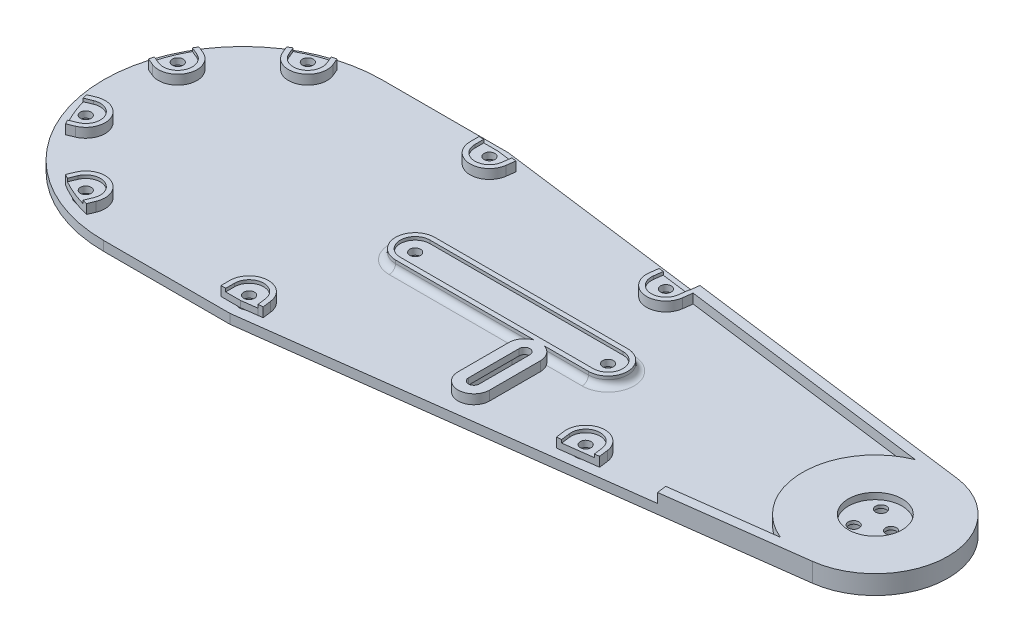
SolidWorks part; units mm, degrees
ref_plane "Front Plane" through (0, 0, 0) normal (0, 0, 1) x (1, 0, 0)
ref_plane "Top Plane" through (0, 0, 0) normal (0, 1, 0) x (1, 0, 0)
ref_plane "Right Plane" through (0, 0, 0) normal (1, 0, 0) x (0, 0, -1)
sketch "Sketch1" plane through (0, 0, 0) normal (0, 1, 0) x (1, 0, 0)
  line L0 (0, 0) -> (200, 0) construction
  line L1 (0, 44) -> (40, 44)
  line L2 (40, 44) -> (202.9659, 22.808)
  line L3 (40, -44) -> (202.9659, -22.808)
  line L4 (0, -44) -> (40, -44)
  line L5 (0, 0) -> (-44, 0) construction
  line L6 (0, 0) -> (-35.1074, 14.542) construction
  line L7 (40, 44) -> (40, -44) construction
  line L8 (44.096, 37.4168) -> (108.6418, 29.0233) construction
  line L9 (109.4155, 34.9732) -> (108.6418, 29.0233) construction
  line L10 (139.1651, -31.1046) -> (137.342, -17.0851) construction
  line L11 (44.2573, -37.3959) -> (129.8631, -26.2637) construction
  arc A0 (0, 44) -> (0, -44) centre (0, 0) ccw
  arc A1 (202.9659, -22.808) -> (202.9659, 22.808) centre (200, 0) ccw
  circle A2 centre (-35.1074, 14.542) radius 1.7
  circle A3 centre (-14.542, 35.1074) radius 1.7
  circle A4 centre (14.542, 35.1074) radius 1.7 [skipped]
  circle A5 centre (35.1074, 14.542) radius 1.7 [skipped]
  circle A6 centre (35.1074, -14.542) radius 1.7 [skipped]
  circle A7 centre (14.542, -35.1074) radius 1.7 [skipped]
  circle A8 centre (-14.542, -35.1074) radius 1.7
  circle A9 centre (-35.1074, -14.542) radius 1.7
  circle A10 centre (200, 0) radius 10.5 construction
  circle A11 centre (40, 38) radius 1.7
  circle A12 centre (40, -38) radius 1.7
  circle A15 centre (40, 38) radius 4.3 construction
  circle A17 centre (40, -38) radius 4.3 construction
  circle A18 centre (134.1272, -25.7092) radius 1.7
  circle A19 centre (134.1272, -25.7092) radius 4.3 construction
  circle A20 centre (87.0602, -31.8298) radius 1.7 construction
  circle A21 centre (104.1794, 29.6036) radius 1.7
  circle A22 centre (104.1794, 29.6036) radius 4.5 construction
  point P29 (0, 0)
  dimension "D1" = 88
  dimension "D3" = 46
  dimension "D6" = 3.4
  dimension "D9" = 21
  dimension "D13" = 9
  dimension "D14" = 8.6
  dimension "D15" = 8.6
  dimension "D18" = 8.6
  dimension "D2" = 200
  dimension "D4" = 40
  dimension "D5" = 22.5
  dimension "D7" = 38
  dimension "D8" = 8
  dimension "D10" = 38
  dimension "D11" = 6
  dimension "D12" = 70
  dimension "D16" = 100
  dimension "D17" = 6
extrude "Boss-Extrude1" add sketch "Sketch1" along normal blind 3
sketch "Sketch2" plane through (0, 3, 0) normal (0, 1, 0) x (1, 0, 0)
  line L0 (202.5533, 19.6347) -> (39.7928, 40.8) construction
  line L1 (39.7928, 40.8) -> (0, 40.8) construction
  line L2 (0, -40.8) -> (39.7928, -40.8) construction
  line L3 (39.7928, -40.8) -> (202.5533, -19.6347) construction
  line L4 (0, -44) -> (40, -44)
  line L5 (40, -44) -> (202.9659, -22.808)
  line L6 (202.9659, 22.808) -> (40, 44)
  line L7 (40, 44) -> (0, 44)
  line L8 (0, -44) -> (40, -44) construction
  line L9 (40, -44) -> (202.9659, -22.808) construction
  line L10 (202.9659, 22.808) -> (40, 44) construction
  line L11 (40, 44) -> (0, 44) construction
  line L12 (-33.3471, 18.7918) -> (-35.6936, 19.7638)
  line L13 (0, 0) -> (-35.1074, 14.542) construction
  line L14 (-36.8678, 10.2921) -> (-39.2143, 11.2641)
  line L15 (-32.7731, 20.1776) -> (-34.9362, 21.0737)
  line L16 (-37.4418, 8.9063) -> (-39.605, 9.8023)
  line L17 (-32.7731, 20.1776) -> (-35.1196, 21.1496) construction
  line L18 (-37.4418, 8.9063) -> (-39.7883, 9.8783) construction
  line L19 (-20.1776, 32.7731) -> (-21.0737, 34.9362)
  line L20 (-8.9063, 37.4418) -> (-9.8023, 39.605)
  line L21 (-10.2921, 36.8678) -> (-11.2641, 39.2143)
  line L22 (-18.7918, 33.3471) -> (-19.7638, 35.6936)
  line L23 (8.9063, 37.4418) -> (9.8023, 39.605) [skipped]
  line L24 (20.1776, 32.7731) -> (21.0737, 34.9362) [skipped]
  line L25 (18.7918, 33.3471) -> (19.7638, 35.6936) [skipped]
  line L26 (10.2921, 36.8678) -> (11.2641, 39.2143) [skipped]
  line L27 (32.7731, 20.1776) -> (34.9362, 21.0737) [skipped]
  line L28 (37.4418, 8.9063) -> (39.605, 9.8023) [skipped]
  line L29 (36.8678, 10.2921) -> (39.2143, 11.2641) [skipped]
  line L30 (33.3471, 18.7918) -> (35.6936, 19.7638) [skipped]
  line L31 (37.4418, -8.9063) -> (39.605, -9.8023) [skipped]
  line L32 (32.7731, -20.1776) -> (34.9362, -21.0737) [skipped]
  line L33 (33.3471, -18.7918) -> (35.6936, -19.7638) [skipped]
  line L34 (36.8678, -10.2921) -> (39.2143, -11.2641) [skipped]
  line L35 (20.1776, -32.7731) -> (21.0737, -34.9362) [skipped]
  line L36 (8.9063, -37.4418) -> (9.8023, -39.605) [skipped]
  line L37 (10.2921, -36.8678) -> (11.2641, -39.2143) [skipped]
  line L38 (18.7918, -33.3471) -> (19.7638, -35.6936) [skipped]
  line L39 (-8.9063, -37.4418) -> (-9.8023, -39.605)
  line L40 (-20.1776, -32.7731) -> (-21.0737, -34.9362)
  line L41 (-18.7918, -33.3471) -> (-19.7638, -35.6936)
  line L42 (-10.2921, -36.8678) -> (-11.2641, -39.2143)
  line L43 (-32.7731, -20.1776) -> (-34.9362, -21.0737)
  line L44 (-37.4418, -8.9063) -> (-39.605, -9.8023)
  line L45 (-36.8678, -10.2921) -> (-39.2143, -11.2641)
  line L46 (-33.3471, -18.7918) -> (-35.6936, -19.7638)
  line L47 (0, 0) -> (200, 0) construction
  line L48 (40, 44) -> (40, 0) construction
  line L49 (44.5616, 37.4068) -> (44.9162, 40.1338)
  line L50 (35.4, 38) -> (35.4, 40.8)
  line L51 (99.6178, 30.1968) -> (99.9789, 32.9734)
  line L52 (108.741, 29.0104) -> (109.1021, 31.787)
  line L55 (129.5656, -26.3024) -> (129.9267, -29.079)
  line L56 (138.6888, -25.116) -> (139.0499, -27.8926)
  line L57 (33.9, 38) -> (33.9, 40.8)
  line L58 (46.0491, 37.2134) -> (46.4037, 39.9403)
  line L59 (98.1303, 30.3902) -> (98.4914, 33.1669)
  line L60 (110.2285, 28.817) -> (110.5895, 31.5936)
  line L61 (140.1763, -24.9226) -> (140.5374, -27.6992)
  line L62 (128.0782, -26.4958) -> (128.4392, -29.2724)
  line L65 (33.9, 40.8) -> (35.4, 40.8)
  line L66 (44.9162, 40.1338) -> (46.4037, 39.9403)
  line L67 (44.5616, -37.4068) -> (44.9162, -40.1338)
  line L68 (35.4, -38) -> (35.4, -40.8)
  line L69 (33.9, -40.8) -> (35.4, -40.8)
  line L70 (33.9, -38) -> (33.9, -40.8)
  line L71 (46.0491, -37.2134) -> (46.4037, -39.9403)
  line L72 (44.9162, -40.1338) -> (46.4037, -39.9403)
  line L75 (128.4392, -29.2724) -> (129.9267, -29.079)
  line L76 (139.0499, -27.8926) -> (140.5374, -27.6992)
  line L77 (98.4914, 33.1669) -> (99.9789, 32.9734)
  line L78 (109.1021, 31.787) -> (110.5895, 31.5936)
  arc A0 (0, 40.8) -> (0, -40.8) centre (0, 0) ccw construction
  arc A1 (-36.8678, 10.2921) -> (-33.3471, 18.7918) centre (-35.1074, 14.542) ccw
  arc A2 (0, 44) -> (0, -44) centre (0, 0) ccw
  arc A3 (202.9659, -22.808) -> (202.9659, 22.808) centre (200, 0) ccw
  arc A5 (0, 44) -> (0, -44) centre (0, 0) ccw construction
  arc A6 (-37.4418, 8.9063) -> (-32.7731, 20.1776) centre (-35.1074, 14.542) ccw
  arc A7 (-39.605, 9.8023) -> (-39.2143, 11.2641) centre (0, 0) cw
  arc A8 (-34.9362, 21.0737) -> (-35.6936, 19.7638) centre (0, 0) ccw
  arc A9 (-21.0737, 34.9362) -> (-19.7638, 35.6936) centre (0, 0) cw
  arc A10 (-20.1776, 32.7731) -> (-8.9063, 37.4418) centre (-14.542, 35.1074) ccw
  arc A11 (-9.8023, 39.605) -> (-11.2641, 39.2143) centre (0, 0) ccw
  arc A12 (-18.7918, 33.3471) -> (-10.2921, 36.8678) centre (-14.542, 35.1074) ccw
  arc A13 (9.8023, 39.605) -> (11.2641, 39.2143) centre (0, 0) cw [skipped]
  arc A14 (8.9063, 37.4418) -> (20.1776, 32.7731) centre (14.542, 35.1074) ccw [skipped]
  arc A15 (21.0737, 34.9362) -> (19.7638, 35.6936) centre (0, 0) ccw [skipped]
  arc A16 (10.2921, 36.8678) -> (18.7918, 33.3471) centre (14.542, 35.1074) ccw [skipped]
  arc A17 (34.9362, 21.0737) -> (35.6936, 19.7638) centre (0, 0) cw [skipped]
  arc A18 (32.7731, 20.1776) -> (37.4418, 8.9063) centre (35.1074, 14.542) ccw [skipped]
  arc A19 (39.605, 9.8023) -> (39.2143, 11.2641) centre (0, 0) ccw [skipped]
  arc A20 (33.3471, 18.7918) -> (36.8678, 10.2921) centre (35.1074, 14.542) ccw [skipped]
  arc A21 (39.605, -9.8023) -> (39.2143, -11.2641) centre (0, 0) cw [skipped]
  arc A22 (37.4418, -8.9063) -> (32.7731, -20.1776) centre (35.1074, -14.542) ccw [skipped]
  arc A23 (34.9362, -21.0737) -> (35.6936, -19.7638) centre (0, 0) ccw [skipped]
  arc A24 (36.8678, -10.2921) -> (33.3471, -18.7918) centre (35.1074, -14.542) ccw [skipped]
  arc A25 (21.0737, -34.9362) -> (19.7638, -35.6936) centre (0, 0) cw [skipped]
  arc A26 (20.1776, -32.7731) -> (8.9063, -37.4418) centre (14.542, -35.1074) ccw [skipped]
  arc A27 (9.8023, -39.605) -> (11.2641, -39.2143) centre (0, 0) ccw [skipped]
  arc A28 (18.7918, -33.3471) -> (10.2921, -36.8678) centre (14.542, -35.1074) ccw [skipped]
  arc A29 (-9.8023, -39.605) -> (-11.2641, -39.2143) centre (0, 0) cw
  arc A30 (-8.9063, -37.4418) -> (-20.1776, -32.7731) centre (-14.542, -35.1074) ccw
  arc A31 (-21.0737, -34.9362) -> (-19.7638, -35.6936) centre (0, 0) ccw
  arc A32 (-10.2921, -36.8678) -> (-18.7918, -33.3471) centre (-14.542, -35.1074) ccw
  arc A33 (-34.9362, -21.0737) -> (-35.6936, -19.7638) centre (0, 0) cw
  arc A34 (-32.7731, -20.1776) -> (-37.4418, -8.9063) centre (-35.1074, -14.542) ccw
  arc A35 (-39.605, -9.8023) -> (-39.2143, -11.2641) centre (0, 0) ccw
  arc A36 (-33.3471, -18.7918) -> (-36.8678, -10.2921) centre (-35.1074, -14.542) ccw
  arc A37 (35.4, 38) -> (44.5616, 37.4068) centre (40, 38) ccw
  circle A38 centre (40, 38) radius 1.7 construction
  arc A39 (99.6178, 30.1968) -> (108.741, 29.0104) centre (104.1794, 29.6036) ccw
  arc A41 (138.6888, -25.116) -> (129.5656, -26.3024) centre (134.1272, -25.7092) ccw
  arc A42 (33.9, 38) -> (46.0491, 37.2134) centre (40, 38) ccw
  arc A43 (98.1303, 30.3902) -> (110.2285, 28.817) centre (104.1794, 29.6036) ccw
  arc A44 (140.1763, -24.9226) -> (128.0782, -26.4958) centre (134.1272, -25.7092) ccw
  arc A46 (35.4, -38) -> (44.5616, -37.4068) centre (40, -38) cw
  arc A47 (33.9, -38) -> (46.0491, -37.2134) centre (40, -38) cw
  point P109 (0, 0)
  dimension "D3" = 9.2
  dimension "D1" = 0
  dimension "D2" = 3.2
  dimension "D4" = 1.5
  dimension "D6" = 1.5
  dimension "D5" = 8
extrude "Boss-Extrude2" add sketch "Sketch2" along normal blind 3
sketch "Sketch3" plane through (0, 3, 0) normal (0, 1, 0) x (1, 0, 0)
  line L0 (-36.8678, 10.2921) -> (-39.2143, 11.2641) construction
  line L1 (-35.6936, 19.7638) -> (-33.3471, 18.7918) construction
  line L2 (-36.8678, 10.2921) -> (-39.2143, 11.2641)
  line L3 (-35.6936, 19.7638) -> (-33.3471, 18.7918)
  line L4 (-11.2641, 39.2143) -> (-10.2921, 36.8678)
  line L5 (-18.7918, 33.3471) -> (-19.7638, 35.6936)
  line L6 (19.7638, 35.6936) -> (18.7918, 33.3471) [skipped]
  line L7 (10.2921, 36.8678) -> (11.2641, 39.2143) [skipped]
  line L8 (39.2143, 11.2641) -> (36.8678, 10.2921) [skipped]
  line L9 (33.3471, 18.7918) -> (35.6936, 19.7638) [skipped]
  line L10 (35.6936, -19.7638) -> (33.3471, -18.7918) [skipped]
  line L11 (36.8678, -10.2921) -> (39.2143, -11.2641) [skipped]
  line L12 (11.2641, -39.2143) -> (10.2921, -36.8678) [skipped]
  line L13 (18.7918, -33.3471) -> (19.7638, -35.6936) [skipped]
  line L14 (-19.7638, -35.6936) -> (-18.7918, -33.3471)
  line L15 (-10.2921, -36.8678) -> (-11.2641, -39.2143)
  line L16 (-39.2143, -11.2641) -> (-36.8678, -10.2921)
  line L17 (-33.3471, -18.7918) -> (-35.6936, -19.7638)
  line L18 (138.6888, -25.116) -> (139.0499, -27.8926) construction
  line L19 (129.9267, -29.079) -> (129.5656, -26.3024) construction
  line L20 (109.1021, 31.787) -> (108.741, 29.0104) construction
  line L21 (99.6178, 30.1968) -> (99.9789, 32.9734) construction
  line L24 (44.5616, -37.4068) -> (44.9162, -40.1338) construction
  line L25 (35.4, -40.8) -> (35.4, -38) construction
  line L26 (44.9162, 40.1338) -> (44.5616, 37.4068) construction
  line L27 (35.4, 38) -> (35.4, 40.8) construction
  line L28 (138.6888, -25.116) -> (139.0499, -27.8926)
  line L29 (129.9267, -29.079) -> (129.5656, -26.3024)
  line L30 (109.1021, 31.787) -> (108.741, 29.0104)
  line L31 (99.6178, 30.1968) -> (99.9789, 32.9734)
  line L34 (44.5616, -37.4068) -> (44.9162, -40.1338)
  line L35 (35.4, -40.8) -> (35.4, -38)
  line L36 (44.9162, 40.1338) -> (44.5616, 37.4068)
  line L37 (35.4, 38) -> (35.4, 40.8)
  line L39 (129.9267, -29.079) -> (139.0499, -27.8926)
  line L40 (99.9789, 32.9734) -> (109.1021, 31.787)
  line L41 (35.4, -40.8) -> (40, -40.8)
  line L42 (40, -40.8) -> (44.9162, -40.1338)
  line L43 (40, -38) -> (40, -40.8) construction
  line L44 (35.4, 40.8) -> (40, 40.8)
  line L45 (40, 40.8) -> (44.9162, 40.1338)
  line L46 (40, 38) -> (40, 40.8) construction
  arc A0 (-36.8678, 10.2921) -> (-33.3471, 18.7918) centre (-35.1074, 14.542) ccw construction
  arc A1 (-36.8678, 10.2921) -> (-33.3471, 18.7918) centre (-35.1074, 14.542) ccw
  arc A2 (-39.2143, 11.2641) -> (-35.6936, 19.7638) centre (0, 0) cw
  circle A3 centre (-35.1074, 14.542) radius 1.7 construction
  circle A4 centre (-35.1074, 14.542) radius 1.7
  arc A5 (-18.7918, 33.3471) -> (-10.2921, 36.8678) centre (-14.542, 35.1074) ccw
  arc A6 (-19.7638, 35.6936) -> (-11.2641, 39.2143) centre (0, 0) cw
  circle A7 centre (-14.542, 35.1074) radius 1.7
  arc A8 (10.2921, 36.8678) -> (18.7918, 33.3471) centre (14.542, 35.1074) ccw [skipped]
  arc A9 (11.2641, 39.2143) -> (19.7638, 35.6936) centre (0, 0) cw [skipped]
  circle A10 centre (14.542, 35.1074) radius 1.7 [skipped]
  arc A11 (33.3471, 18.7918) -> (36.8678, 10.2921) centre (35.1074, 14.542) ccw [skipped]
  arc A12 (35.6936, 19.7638) -> (39.2143, 11.2641) centre (0, 0) cw [skipped]
  circle A13 centre (35.1074, 14.542) radius 1.7 [skipped]
  arc A14 (36.8678, -10.2921) -> (33.3471, -18.7918) centre (35.1074, -14.542) ccw [skipped]
  arc A15 (39.2143, -11.2641) -> (35.6936, -19.7638) centre (0, 0) cw [skipped]
  circle A16 centre (35.1074, -14.542) radius 1.7 [skipped]
  arc A17 (18.7918, -33.3471) -> (10.2921, -36.8678) centre (14.542, -35.1074) ccw [skipped]
  arc A18 (19.7638, -35.6936) -> (11.2641, -39.2143) centre (0, 0) cw [skipped]
  circle A19 centre (14.542, -35.1074) radius 1.7 [skipped]
  arc A20 (-10.2921, -36.8678) -> (-18.7918, -33.3471) centre (-14.542, -35.1074) ccw
  arc A21 (-11.2641, -39.2143) -> (-19.7638, -35.6936) centre (0, 0) cw
  circle A22 centre (-14.542, -35.1074) radius 1.7
  arc A23 (-33.3471, -18.7918) -> (-36.8678, -10.2921) centre (-35.1074, -14.542) ccw
  arc A24 (-35.6936, -19.7638) -> (-39.2143, -11.2641) centre (0, 0) cw
  circle A25 centre (-35.1074, -14.542) radius 1.7
  arc A26 (138.6888, -25.116) -> (129.5656, -26.3024) centre (134.1272, -25.7092) ccw construction
  arc A27 (99.6178, 30.1968) -> (108.741, 29.0104) centre (104.1794, 29.6036) ccw construction
  arc A29 (44.5616, -37.4068) -> (35.4, -38) centre (40, -38) ccw construction
  arc A30 (35.4, 38) -> (44.5616, 37.4068) centre (40, 38) ccw construction
  arc A31 (138.6888, -25.116) -> (129.5656, -26.3024) centre (134.1272, -25.7092) ccw
  arc A32 (99.6178, 30.1968) -> (108.741, 29.0104) centre (104.1794, 29.6036) ccw
  arc A34 (44.5616, -37.4068) -> (35.4, -38) centre (40, -38) ccw
  arc A35 (35.4, 38) -> (44.5616, 37.4068) centre (40, 38) ccw
  circle A36 centre (40, -38) radius 1.7 construction
  circle A38 centre (134.1272, -25.7092) radius 1.7 construction
  circle A39 centre (104.1794, 29.6036) radius 1.7 construction
  circle A40 centre (40, 38) radius 1.7 construction
  circle A41 centre (40, -38) radius 1.7
  circle A43 centre (134.1272, -25.7092) radius 1.7
  circle A44 centre (104.1794, 29.6036) radius 1.7
  circle A45 centre (40, 38) radius 1.7
  point P62 (0, 0)
  dimension "D1" = 8
extrude "Boss-Extrude3" add sketch "Sketch3" along normal blind 2
sketch "Sketch4" plane through (0, 0, 0) normal (0, -1, 0) x (1, 0, 0)
  circle A0 centre (-14.542, 35.1074) radius 3
  circle A1 centre (-35.1074, 14.542) radius 3
  circle A2 centre (-35.1074, -14.542) radius 3
  circle A3 centre (-14.542, -35.1074) radius 3
  circle A4 centre (40, 38) radius 3
  circle A6 centre (134.1272, 25.7092) radius 3
  circle A7 centre (104.1794, -29.6036) radius 3
  circle A8 centre (40, -38) radius 3
  dimension "D1" = 6
extrude "Cut-Extrude1" cut sketch "Sketch4" against normal blind 3
sketch "Sketch5" plane through (0, 3, 0) normal (0, 1, 0) x (1, 0, 0)
  circle A0 centre (200, 0) radius 8.5
  dimension "D1" = 17
extrude "Cut-Extrude2" cut sketch "Sketch5" against normal offset from surface (1 mm away) 2 up to face at (-35.1074, 0, 11.542)
sketch "Sketch6" plane through (0, 3, 0) normal (0, 1, 0) x (1, 0, 0)
  line L0 (40, -44) -> (159.5853, -28.4492) construction
  line L1 (40, -44) -> (202.9659, -22.808) construction
  line L2 (40, 44) -> (109.6139, 34.9474) construction
  line L3 (202.9659, 22.808) -> (40, 44) construction
  line L4 (159.5853, -28.4492) -> (159.1985, -25.4742)
  line L6 (159.5853, -28.4492) -> (202.9659, -22.808)
  line L10 (159.1985, -25.4742) -> (191.3161, -21.2976)
  line L11 (109.6139, 34.9474) -> (202.9659, 22.808)
  line L12 (109.6139, 34.9474) -> (109.227, 31.9725)
  line L13 (109.227, 31.9725) -> (109.1278, 31.9854)
  line L14 (109.1021, 31.787) -> (109.1278, 31.9854)
  line L15 (109.1021, 31.787) -> (110.5895, 31.5936)
  line L16 (110.5895, 31.5936) -> (110.6153, 31.7919)
  line L17 (110.6153, 31.7919) -> (191.3161, 21.2976)
  line L18 (200, 0) -> (200, -24) construction
  line L19 (200, -24) -> (93.458, -24) construction
  line L20 (159.387, -28.475) -> (159.0002, -25.5) construction
  circle A0 centre (200, 0) radius 8.5 construction
  circle A1 centre (200, 0) radius 8.5
  arc A2 (202.9659, -22.808) -> (202.9659, 22.808) centre (200, 0) ccw
  arc A3 (202.9659, -22.808) -> (202.9659, 22.808) centre (200, 0) ccw construction
  arc A4 (191.3161, 21.2976) -> (191.3161, -21.2976) centre (200, 0) ccw
  dimension "D1" = 1.5
  dimension "D2" = 70.2
  dimension "D3" = 3
  dimension "D4" = 3
  dimension "D5" = 24
  dimension "D6" = 0.2
extrude "Boss-Extrude4" add sketch "Sketch6" along normal blind 3
sketch "Sketch8" plane through (0, 3, 0) normal (0, 1, 0) x (1, 0, 0)
  line L0 (0, 0) -> (200, 0) construction
  line L1 (85, 0) -> (85, -4.7) construction
  line L6 (54.5, 4.7) -> (115.5, 4.7)
  line L8 (54.5, -4.7) -> (115.5, -4.7)
  line L9 (54.5, 6.2) -> (115.5, 6.2)
  line L10 (54.5, -6.2) -> (115.5, -6.2)
  line L11 (49.8, 0) -> (49.8, 12.6427) construction
  arc A1 (54.5, 4.7) -> (54.5, -4.7) centre (54.5, 0) ccw
  arc A2 (115.5, 4.7) -> (115.5, -4.7) centre (115.5, 0) cw
  arc A3 (115.5, 6.2) -> (115.5, -6.2) centre (115.5, 0) cw
  arc A4 (54.5, 6.2) -> (54.5, -6.2) centre (54.5, 0) ccw
  point P4 (85, 0)
  point P15 (85, 4.7)
  point P17 (85, -4.7)
  dimension "D1" = 9.4
  dimension "D2" = 85
  dimension "D3" = 35.2
  dimension "D4" = 1.5
extrude "Boss-Extrude6" add sketch "Sketch8" along normal blind 3
fillet "Fillet2" radius 2 4 edges at (48.3, 3, 0) (85, 3, -6.2) (121.7, 3, 0) (85, 3, 6.2)
sketch "Sketch10" plane through (0, 3, 0) normal (0, 1, 0) x (1, 0, 0)
  line L2 (54.5, -4.7) -> (115.5, -4.7)
  line L6 (54.5, -4.7) -> (115.5, -4.7)
  line L7 (115.5, 4.7) -> (54.5, 4.7)
  line L8 (115.5, 4.7) -> (54.5, 4.7)
  arc A2 (54.5, 4.7) -> (54.5, -4.7) centre (54.5, 0) ccw
  arc A6 (54.5, 4.7) -> (54.5, -4.7) centre (54.5, 0) ccw
  arc A8 (115.5, -4.7) -> (115.5, 4.7) centre (115.5, 0) ccw
  arc A9 (115.5, -4.7) -> (115.5, 4.7) centre (115.5, 0) ccw
  dimension "D1" = 0
extrude "Boss-Extrude7" add sketch "Sketch10" along normal blind 2
sketch "Sketch9" plane through (0, 3, 0) normal (0, 1, 0) x (1, 0, 0)
  line L0 (49.8, 0) -> (120.2, 0) construction
  line L1 (85, 0) -> (85, 13.5194) construction
  arc A2 (54.5, 4.7) -> (54.5, -4.7) centre (54.5, 0) ccw construction
  arc A3 (115.5, -4.7) -> (115.5, 4.7) centre (115.5, 0) ccw construction
  circle A4 centre (54.5, 0) radius 1.7
  circle A5 centre (115.5, 0) radius 1.7
  dimension "D1" = 30.5
  dimension "D2" = 3.4
extrude "Cut-Extrude3" cut sketch "Sketch9" against normal through all and the other way through all
sketch "Sketch11" plane through (0, 0, 0) normal (0, -1, 0) x (1, 0, 0)
  circle A0 centre (54.5, 0) radius 3
  circle A1 centre (115.5, 0) radius 3
  dimension "D1" = 6
extrude "Cut-Extrude4" cut sketch "Sketch11" against normal blind 3
sketch "Sketch12" plane through (0, 2, 0) normal (0, 1, 0) x (1, 0, 0)
  circle A1 centre (200, 0) radius 8.5
  circle A2 centre (200, 0) radius 8.5
  dimension "D1" = 0
extrude "Boss-Extrude8" add sketch "Sketch12" along normal blind 2
sketch "Sketch13" plane through (0, 4, 0) normal (0, 1, 0) x (1, 0, 0)
  line L0 (200, 0) -> (205, 0) construction
  circle A0 centre (205, 0) radius 1.7
  circle A1 centre (197.5, -4.3301) radius 1.7
  circle A2 centre (197.5, 4.3301) radius 1.7
  point P11 (200, 0)
  dimension "D1" = 3.4
  dimension "D2" = 5
  dimension "D3" = 3
extrude "Cut-Extrude5" cut sketch "Sketch13" against normal up to next
sketch "Sketch14" plane through (0, 0, 0) normal (0, -1, 0) x (1, 0, 0)
  circle A0 centre (197.5, 4.3301) radius 3
  circle A1 centre (205, 0) radius 3
  circle A2 centre (197.5, -4.3301) radius 3
  dimension "D1" = 6
extrude "Cut-Extrude6" cut sketch "Sketch14" against normal blind 3
sketch "Sketch15" plane through (0, 3, 0) normal (0, 1, 0) x (1, 0, 0)
  line L0 (0, 0) -> (200, 0) construction
  line L1 (159.1985, -25.4742) -> (75.4221, -36.3685) construction
  line L3 (100, 0) -> (100, -4.7) construction
  line L4 (191.3161, -21.2976) -> (159.1985, -25.4742) construction
  line L5 (100, -10.9362) -> (100, -26.9362) construction
  line L6 (101.7, -10.9362) -> (101.7, -26.9362)
  line L7 (98.3, -10.9362) -> (98.3, -26.9362)
  line L8 (100, -26.9362) -> (100, -33.1724) construction
  line L10 (54.5, -4.7) -> (115.5, -4.7) construction
  line L11 (100, -4.7) -> (100, -10.9362) construction
  arc A0 (101.7, -10.9362) -> (98.3, -10.9362) centre (100, -10.9362) ccw
  arc A1 (98.3, -26.9362) -> (101.7, -26.9362) centre (100, -26.9362) ccw
  point P9 (100, -18.9362)
  dimension "D1" = 3.4
  dimension "D2" = 16
extrude "Cut-Extrude7" cut sketch "Sketch15" against normal through all
sketch "Sketch16" plane through (0, 3, 0) normal (0, 1, 0) x (1, 0, 0)
  line L5 (100, -10.9362) -> (100, -26.9362) construction
  line L6 (98.3, -10.9362) -> (98.3, -26.9362) construction
  line L7 (101.7, -26.9362) -> (101.7, -10.9362) construction
  line L8 (98.3, -10.9362) -> (98.3, -26.9362)
  line L9 (95, -10.9362) -> (95, -26.9362)
  line L10 (105, -26.9362) -> (105, -10.9362)
  line L11 (101.7, -26.9362) -> (101.7, -10.9362)
  arc A5 (98.3, -26.9362) -> (101.7, -26.9362) centre (100, -26.9362) ccw construction
  arc A6 (101.7, -10.9362) -> (98.3, -10.9362) centre (100, -10.9362) ccw construction
  arc A7 (98.3, -26.9362) -> (101.7, -26.9362) centre (100, -26.9362) ccw
  arc A8 (101.7, -10.9362) -> (98.3, -10.9362) centre (100, -10.9362) ccw
  arc A9 (95, -26.9362) -> (105, -26.9362) centre (100, -26.9362) ccw
  arc A10 (105, -10.9362) -> (95, -10.9362) centre (100, -10.9362) ccw
  dimension "D1" = 10
extrude "Boss-Extrude9" add sketch "Sketch16" along normal blind 3
sketch "Sketch17" plane through (0, 0, 0) normal (0, -1, 0) x (1, 0, 0)
  line L6 (100, 26.9362) -> (100, 10.9362) construction
  line L10 (96, 26.9362) -> (96, 10.9362)
  line L11 (104, 10.9362) -> (104, 26.9362)
  arc A4 (101.7, 26.9362) -> (98.3, 26.9362) centre (100, 26.9362) ccw construction
  arc A5 (98.3, 10.9362) -> (101.7, 10.9362) centre (100, 10.9362) ccw construction
  arc A8 (96, 10.9362) -> (104, 10.9362) centre (100, 10.9362) ccw
  arc A9 (104, 26.9362) -> (96, 26.9362) centre (100, 26.9362) ccw
  dimension "D1" = 8
extrude "Cut-Extrude8" cut sketch "Sketch17" against normal blind 4
